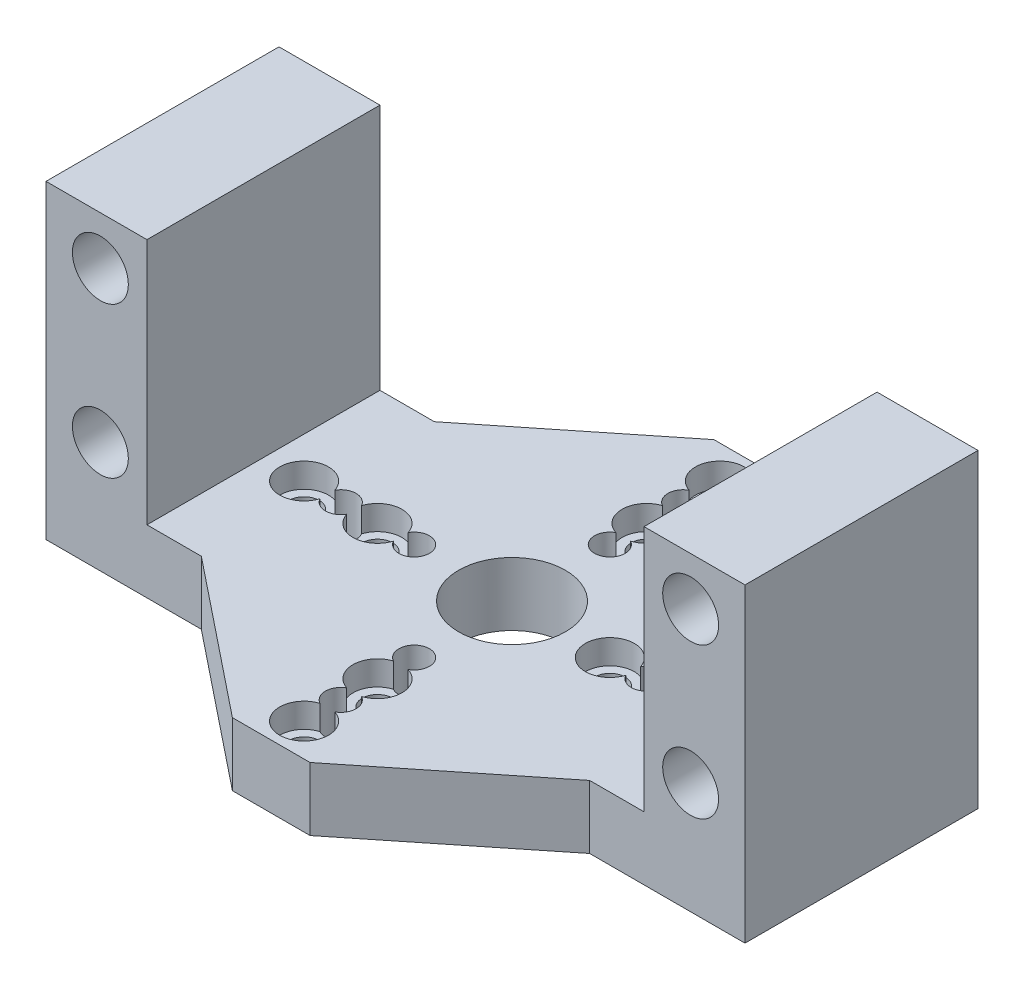
SolidWorks part; units mm, degrees
ref_plane "Front" through (0, 0, 0) normal (0, 0, 1) x (1, 0, 0)
ref_plane "Top" through (0, 0, 0) normal (0, 1, 0) x (1, 0, 0)
ref_plane "Right" through (0, 0, 0) normal (1, 0, 0) x (0, 0, -1)
sketch "Sketch1" plane through (0, 0, 0) normal (0, 0, 1) x (1, 0, 0)
  line L0 (8.255, 25.368) -> (8.255, 5.175)
  line L1 (0, 0) -> (57.15, 0)
  line L2 (0, 0) -> (0, 25.368)
  line L3 (0, 25.368) -> (8.255, 25.368)
  line L4 (57.15, 0) -> (57.15, 25.368)
  line L5 (8.255, 5.175) -> (48.895, 5.175)
  line L6 (48.895, 5.175) -> (48.895, 25.368)
  line L7 (48.895, 25.368) -> (57.15, 25.368)
  line L8 (28.575, 5.175) -> (28.575, 0) construction
  circle A0 centre (4.445, 21.431) radius 2.286
  circle A1 centre (4.445, 9.112) radius 2.286
  circle A2 centre (52.705, 9.112) radius 2.286
  circle A3 centre (52.705, 21.431) radius 2.286
  dimension "D5" = 3.937
  dimension "D6" = 4.572
  dimension "D8" = 3.937
  dimension "D1" = 8.255
  dimension "D2" = 40.64
  dimension "D3" = 5.175
  dimension "D4" = 20.193
  dimension "D7" = 3.81
extrude "Boss-Extrude1" add sketch "Sketch1" along normal blind 19.05
sketch "Sketch2" plane through (0, 0, 0) normal (0, -1, 0) x (1, 0, 0)
  line L0 (28.575, 19.05) -> (28.575, 0) construction
  line L1 (0, 19.05) -> (57.15, 19.05) construction
  line L2 (0, 0) -> (57.15, 0) construction
  line L3 (57.15, 9.525) -> (0, 9.525) construction
  line L4 (57.15, 19.05) -> (57.15, 0) construction
  line L5 (0, 19.05) -> (0, 0) construction
  circle A0 centre (36.575, 9.525) radius 1.25
  circle A1 centre (39.575, 9.525) radius 1.25
  circle A2 centre (42.575, 9.525) radius 1.25
  circle A3 centre (45.575, 9.525) radius 1.25
  circle A4 centre (28.575, 1.525) radius 1.25
  circle A5 centre (28.575, -1.475) radius 1.25
  circle A6 centre (28.575, -4.475) radius 1.25
  circle A7 centre (28.575, -7.475) radius 1.25
  circle A8 centre (20.575, 9.525) radius 1.25
  circle A9 centre (17.575, 9.525) radius 1.25
  circle A10 centre (14.575, 9.525) radius 1.25
  circle A11 centre (11.575, 9.525) radius 1.25
  circle A12 centre (28.575, 17.525) radius 1.25
  circle A13 centre (28.575, 20.525) radius 1.25
  circle A14 centre (28.575, 23.525) radius 1.25
  circle A15 centre (28.575, 26.525) radius 1.25
  circle A16 centre (28.575, 9.525) radius 4.3656
  point P47 (28.575, 9.525)
  dimension "D5" = 2.5
  dimension "D7" = 8.7312
  dimension "D1" = 8
  dimension "D2" = 11
  dimension "D3" = 14
  dimension "D4" = 17
  dimension "D6" = 4
sketch "Sketch3" plane through (0, 0, 0) normal (0, -1, 0) x (1, 0, 0)
  line L0 (0, 19.05) -> (57.15, 19.05) construction
  line L1 (25.4, 19.05) -> (31.75, 19.05) construction
  line L2 (25.4, 19.05) -> (25.4, 29.21) construction
  line L3 (25.4, 29.21) -> (31.75, 29.21)
  line L4 (31.75, 19.05) -> (31.75, 29.21) construction
  line L5 (25.4, 29.21) -> (12.7, 19.05)
  line L6 (31.75, 29.21) -> (44.45, 19.05)
  line L7 (0, 9.525) -> (57.15, 9.525) construction
  line L8 (31.75, -10.16) -> (44.45, 0)
  line L9 (25.4, -10.16) -> (12.7, 0)
  line L10 (25.4, -10.16) -> (31.75, -10.16)
  line L11 (12.7, 19.05) -> (12.7, 0)
  line L12 (44.45, 19.05) -> (44.45, 0)
  point P11 (28.575, 19.05)
  point P12 (28.575, 29.21)
  dimension "D1" = 6.35
  dimension "D2" = 10.16
  dimension "D3" = 12.7
extrude "Boss-Extrude2" add sketch "Sketch3" against normal up to surface (5.175 mm away) up to face at (28.575, 5.175, 9.525)
extrude "Cut-Extrude1" cut sketch "Sketch2" against normal up to surface (5.175 mm away) up to face at (28.575, 5.175, 9.525)
sketch "Sketch4" plane through (0, 5.175, 0) normal (0, 1, 0) x (1, 0, 0)
  circle A0 centre (28.575, 1.475) radius 2
  circle A2 centre (28.575, 7.475) radius 2
  circle A3 centre (11.575, -9.525) radius 2
  circle A4 centre (17.575, -9.525) radius 2
  circle A6 centre (36.575, -9.525) radius 2
  circle A11 centre (28.575, -20.525) radius 2
  circle A12 centre (45.575, -9.525) radius 2
  circle A13 centre (28.575, -26.525) radius 2
  dimension "D1" = 4
extrude "Cut-Extrude2" cut sketch "Sketch4" against normal blind 2
